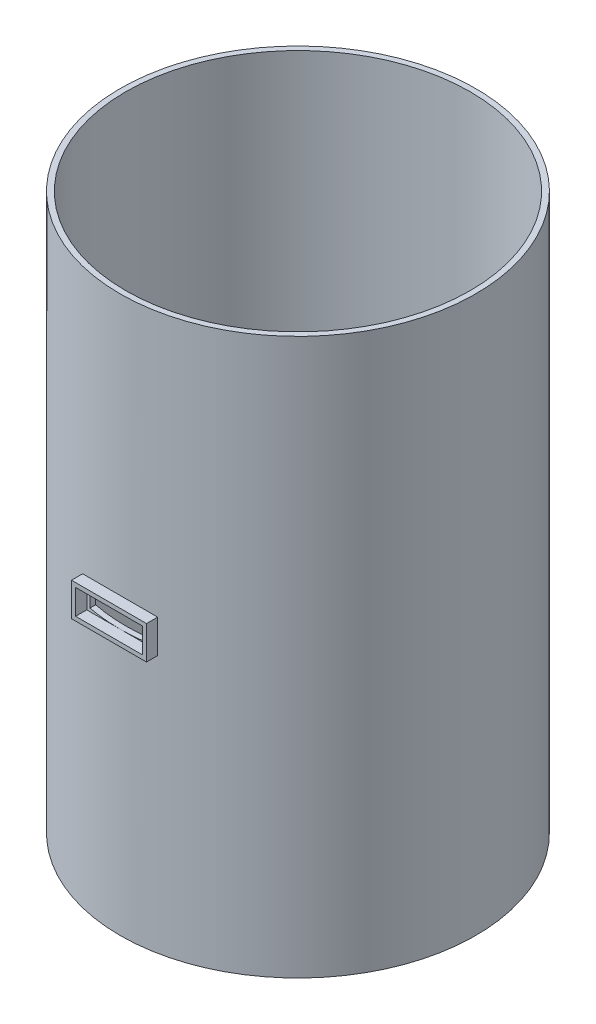
SolidWorks part; units mm, degrees
ref_plane "Front Plane" through (0, 0, 0) normal (0, 0, 1) x (1, 0, 0)
ref_plane "Top Plane" through (0, 0, 0) normal (0, 1, 0) x (1, 0, 0)
ref_plane "Right Plane" through (0, 0, 0) normal (1, 0, 0) x (0, 0, -1)
sketch "Sketch1" plane through (0, 0, 0) normal (0, 1, 0) x (1, 0, 0)
  circle A0 centre (0, 0) radius 32
  circle A1 centre (0, 0) radius 31
  dimension "D1" = 64
  dimension "D2" = 62
extrude "Boss-Extrude1" add sketch "Sketch1" along normal blind 100 contours A0 | A1
ref_plane "Plane1" through (0, 0, 32) normal (0, 0, 1) x (1, 0, 0)
sketch "Sketch2" plane through (0, 0, 32) normal (0, 0, 1) x (1, 0, 0)
  line L0 (32, 50) -> (-32, 50) construction
  line L1 (32, 0) -> (32, 100) construction
  line L2 (-32, 100) -> (-32, 0) construction
  line L3 (0, 100) -> (0, 0) construction
  line L4 (31, 100) -> (-31, 100) construction
  line L6 (-6, 52.25) -> (6, 52.25)
  line L7 (-6, 52.25) -> (-6, 47.75)
  line L8 (-6, 47.75) -> (6, 47.75)
  line L9 (6, 52.25) -> (6, 47.75)
  line L10 (-6, 52.25) -> (6, 47.75) construction
  line L11 (-6, 47.75) -> (6, 52.25) construction
  line L12 (-6.75, 53) -> (6.75, 53)
  line L13 (-6.75, 53) -> (-6.75, 47)
  line L14 (-6.75, 47) -> (6.75, 47)
  line L15 (6.75, 53) -> (6.75, 47)
  line L16 (-6.75, 53) -> (6.75, 47) construction
  line L17 (-6.75, 47) -> (6.75, 53) construction
  point P11 (0, 50)
  point P16 (0, 50)
  point P21 (0, 0)
  point P22 (0, 0)
  point P23 (0, 0)
  dimension "D1" = 4.5
  dimension "D2" = 12
  dimension "D3" = 6
  dimension "D4" = 13.5
extrude "Boss-Extrude2" add sketch "Sketch2" along normal blind 2 separate body contours L6 L9 L8 L7 | L12 L15 L14 L13
sketch "Sketch4" plane through (0, 0, 32) normal (0, 0, 1) x (1, 0, 0)
  line L0 (32, 50) -> (-32, 50) construction
  line L1 (32, 0) -> (32, 100) construction
  line L2 (-32, 100) -> (-32, 0) construction
  line L4 (-6, 52.25) -> (6, 52.25)
  line L5 (-6, 52.25) -> (-6, 47.75)
  line L6 (-6, 47.75) -> (6, 47.75)
  line L7 (6, 52.25) -> (6, 47.75)
  line L8 (-6, 52.25) -> (6, 47.75) construction
  line L9 (-6, 47.75) -> (6, 52.25) construction
  point P6 (0, 50)
extrude "Cut-Extrude1" cut sketch "Sketch4" against normal blind 15 and the other way through all
